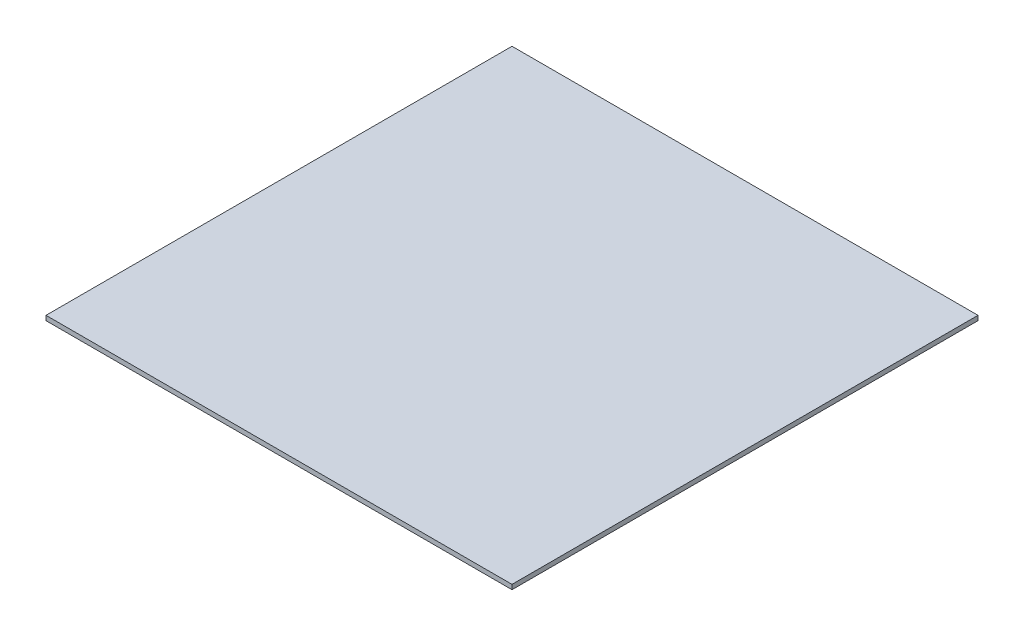
SolidWorks part; units mm, degrees
material "Balsa"
ref_plane "Plan de face" through (0, 0, 0) normal (0, 0, 1) x (1, 0, 0)
ref_plane "Plan de dessus" through (0, 0, 0) normal (0, 1, 0) x (1, 0, 0)
ref_plane "Plan de droite" through (0, 0, 0) normal (1, 0, 0) x (0, 0, -1)
sketch "Esquisse1" plane through (0, 0, 0) normal (0, 1, 0) x (1, 0, 0)
  line L1 (-250, -250) -> (250, -250)
  line L2 (-250, -250) -> (-250, 250)
  line L3 (-250, 250) -> (250, 250)
  line L4 (250, -250) -> (250, 250)
  line L5 (-250, -250) -> (250, 250) construction
  line L6 (-250, 250) -> (250, -250) construction
  point P0 (0, 0)
  dimension "D1" = 500
  dimension "D2" = 500
extrude "Boss.-Extru.1" add sketch "Esquisse1" along normal blind 5
